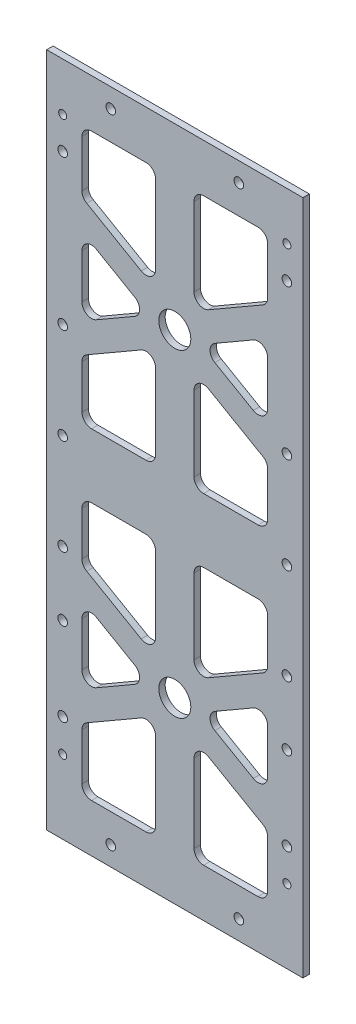
SolidWorks part; units mm, degrees
material "6061-T6 (SS)"
ref_plane "Front Plane" through (0, 0, 0) normal (0, 0, 1) x (1, 0, 0)
ref_plane "Top Plane" through (0, 0, 0) normal (0, 1, 0) x (1, 0, 0)
ref_plane "Right Plane" through (0, 0, 0) normal (1, 0, 0) x (0, 0, -1)
sketch "Sketch1" plane through (0, 0, 0) normal (0, 0, 1) x (1, 0, 0)
  line L1 (0, 0) -> (88, 0)
  line L2 (0, 0) -> (0, 211)
  line L3 (0, 211) -> (88, 211)
  line L4 (88, 0) -> (88, 211)
  dimension "D1" = 88
  dimension "D2" = 211
extrude "Boss-Extrude1" add sketch "Sketch1" along normal blind 2
sketch "Sketch2" plane through (0, 0, 2) normal (0, 0, 1) x (1, 0, 0)
  line L0 (0, 105.5) -> (88, 105.5) construction
  line L1 (0, 211) -> (0, 0) construction
  line L2 (88, 0) -> (88, 211) construction
  line L3 (44, 211) -> (44, 0) construction
  line L4 (88, 211) -> (0, 211) construction
  line L5 (0, 0) -> (88, 0) construction
  line L6 (0, 155.25) -> (88, 155.25) construction
  line L7 (0, 55.75) -> (88, 55.75) construction
  dimension "D1" = 55.75
  dimension "D2" = 55.75
sketch "Sketch3" plane through (0, 0, 2) normal (0, 0, 1) x (1, 0, 0)
  line L0 (0, 155.25) -> (88, 155.25) construction
  line L1 (38, 196) -> (38, 115.5)
  line L2 (0, 211) -> (0, 0) construction
  line L3 (15, 196) -> (73, 196)
  line L4 (15, 196) -> (15, 115.5)
  line L5 (15, 115.5) -> (73, 115.5)
  line L6 (73, 196) -> (73, 115.5)
  line L7 (88, 211) -> (0, 211) construction
  line L8 (88, 0) -> (88, 211) construction
  line L9 (0, 105.5) -> (88, 105.5) construction
  line L13 (73, 171.9932) -> (15, 138.5068) construction
  line L14 (15, 171.9932) -> (73, 138.5068) construction
  line L15 (73, 176.612) -> (15, 143.1256)
  line L16 (73, 167.3744) -> (15, 133.888)
  line L17 (15, 176.612) -> (73, 143.1256)
  line L18 (15, 167.3744) -> (73, 133.888)
  line L19 (50, 196) -> (50, 115.5)
  circle A0 centre (44, 155.25) radius 5
  dimension "D1" = 10
  dimension "D3" = 15
  dimension "D4" = 15
  dimension "D5" = 15
  dimension "D6" = 10
  dimension "D9" = 30
  dimension "D10" = 30
  dimension "D11" = 8
  dimension "D12" = 4
  dimension "D13" = 4
  dimension "D14" = 8
ref_plane "Plane1" through (0, 105.5, 0) normal (0, 1, 0) x (1, 0, 0)
extrude "Cut-Extrude2" cut sketch "Sketch3" against normal blind 2
sketch "Sketch4" plane through (0, 0, 2) normal (0, 0, 1) x (1, 0, 0)
  line L0 (0, 155.25) -> (88, 155.25) construction
  circle A0 centre (44, 155.25) radius 5
  dimension "D1" = 10
extrude "Cut-Extrude3" cut sketch "Sketch4" against normal through all
mirror "Mirror2" about plane through (0, 105.5, 0) normal (0, 1, 0) of "Cut-Extrude2", "Cut-Extrude3"
fillet "Fillet2" radius 3 44 edges at (73, 67.8744, 1) (73, 43.6256, 1) (52, 55.75, 1) (15, 15, 1) (15, 34.388, 1) (15, 143.1256, 1) (15, 167.3744, 1) (36, 155.25, 1) (15, 115.5, 1) (15, 133.888, 1) (73, 196, 1) (73, 115.5, 1) (73, 133.888, 1) (15, 196, 1) (15, 176.612, 1) (73, 167.3744, 1) (73, 143.1256, 1) (52, 155.25, 1) (73, 95.5, 1) (73, 77.112, 1) (73, 34.388, 1) (73, 15, 1) (15, 77.112, 1) (15, 95.5, 1) (15, 43.6256, 1) (15, 67.8744, 1) (36, 55.75, 1) (73, 176.612, 1) (50, 15, 1) (38, 15, 1) (38, 47.6671, 1) (50, 47.6671, 1) (38, 63.8329, 1) (38, 95.5, 1) (50, 63.8329, 1) (50, 95.5, 1) (38, 115.5, 1) (38, 147.1671, 1) (50, 147.1671, 1) (50, 115.5, 1) (38, 196, 1) (38, 163.3329, 1) (50, 163.3329, 1) (50, 196, 1)
sketch "Sketch23" plane through (0, 0, 2) normal (0, 0, 1) x (1, 0, 0)
  line L2 (88, 211) -> (88, 0)
  line L3 (86, 211) -> (86, 0)
  line L4 (86, 211) -> (88, 211)
  line L5 (86, 0) -> (88, 0)
  line L6 (2.1504, 211) -> (2.1504, 0)
  line L7 (2.1504, 211) -> (0, 211)
  line L8 (0, 211) -> (0, 0)
  line L9 (2.1504, 0) -> (0, 0)
  dimension "D1" = 2
extrude "Cut-Extrude5" cut sketch "Sketch23" against normal blind 10 contours L5 L2 L4 L3 | L6 L9 L8 L7
sketch "Sketch29" plane through (0, 0, 0) normal (0, 0, -1) x (-1, 0, 0)
  line L0 (-44, 0) -> (-44, 211)
  line L4 (-86, 105.5) -> (-2.1504, 105.5)
  line L5 (-86, 0) -> (-86, 211) construction
  line L6 (-2.1504, 0) -> (-2.1504, 211) construction
  line L16 (-4, 211) -> (1.9115, 211)
  line L17 (-4, 211) -> (-4, 0)
  line L18 (-4, 0) -> (1.9115, 0)
  line L19 (1.9115, 211) -> (1.9115, 0)
  line L20 (-84, 0) -> (-88.0365, 0)
  line L21 (-84, 0) -> (-84, 211)
  line L22 (-84, 211) -> (-88.0365, 211)
  line L23 (-88.0365, 0) -> (-88.0365, 211)
  point P0 (-44, 155.25)
  point P1 (-44, 217.1483)
  point P3 (-4, 155.25)
  point P4 (-4, 217.1483)
  point P5 (-84, 155.25)
  point P6 (-84, 217.1483)
  point P8 (-4, 105.5)
  point P22 (-84, 105.5)
  point P23 (-44, 105.5)
extrude "Cut-Extrude10" cut sketch "Sketch29" against normal blind 2
sketch "Sketch30" plane through (0, 0, 2) normal (0, 0, 1) x (1, 0, 0)
  line L0 (44, 211) -> (44, 0) construction
  line L1 (84, 211) -> (4, 211) construction
  line L2 (4, 0) -> (84, 0) construction
  line L3 (4, 211) -> (4, 0) construction
  point P8 (64, 6)
  point P9 (79, 23)
  point P10 (79, 33.2)
  point P11 (9, 33.2)
  point P13 (9, 196)
  point P14 (9, 186)
  point P15 (9, 139.2)
  point P16 (9, 109.2)
  point P18 (9, 79.2)
  point P19 (9, 59.2)
  point P20 (79, 59.2)
  point P21 (9, 23)
  point P23 (24, 205)
  point P25 (79, 79.2)
  point P26 (79, 109.2)
  point P27 (24, 6)
  point P29 (79, 139.2)
  point P30 (79, 186)
  point P31 (79, 196)
  point P32 (64, 205)
  dimension "D1" = 20
  dimension "D2" = 6
  dimension "D3" = 5
  dimension "D4" = 15
  dimension "D5" = 25
  dimension "D6" = 71.8
  dimension "D7" = 101.8
  dimension "D8" = 131.8
  dimension "D9" = 151.8
  dimension "D10" = 5
  dimension "D11" = 188
  dimension "D12" = 205
  dimension "D13" = 20
  dimension "D14" = 5
  dimension "D15" = 5
  dimension "D16" = 5
  dimension "D17" = 5
  dimension "D18" = 5
  dimension "D19" = 5
  dimension "D20" = 177.8
hole_wizard "Ø3.0mm Dowel Hole1" positions "Sketch31" profile "Sketch32" hole size "Ø3.0" standard "ANSI Metric" end condition through all
sketch "Sketch31" plane through (0, 0, 2) normal (0, 0, 1) x (1, 0, 0)
  point P0 (24, 205)
  point P3 (64, 205)
  point P6 (9, 186)
  point P9 (79, 186)
  point P12 (9, 139.2)
  point P15 (79, 139.2)
  point P18 (79, 109.2)
  point P21 (9, 109.2)
  point P24 (9, 79.2)
  point P27 (79, 79.2)
  point P30 (79, 59.2)
  point P33 (9, 59.2)
  point P36 (9, 33.2)
  point P39 (79, 33.2)
  point P42 (64, 6)
  point P45 (24, 6)
sketch "Sketch32" plane through (24, 205, 2) normal (1, 0, 0) x (0, -1, 0)
  line L0 (0, 0) -> (0, 2)
  line L1 (0, 2) -> (1.5, 2)
  line L2 (1.5, 2) -> (1.5, 0)
  line L5 (1.5, 0) -> (0, 0)
  line L11 (0, -6.35) -> (0, 107.95) construction
  dimension "Thru Hole Dia." = 3
  dimension "Thru Hole Depth" = 2
hole_wizard "Tap Drill for M3x0.5 Tap1" positions "Sketch33" profile "Sketch34" hole size "M3x0.5" standard "ANSI Metric" end condition through all
sketch "Sketch33" plane through (0, 0, 2) normal (0, 0, 1) x (1, 0, 0)
  point P0 (9, 23)
  point P3 (79, 23)
  point P6 (9, 196)
  point P9 (79, 196)
sketch "Sketch34" plane through (9, 23, 2) normal (1, 0, 0) x (0, -1, 0)
  line L0 (0, 0) -> (0, 2)
  line L1 (0, 2) -> (1.25, 2)
  line L2 (1.25, 2) -> (1.25, 0)
  line L5 (1.25, 0) -> (0, 0)
  line L11 (0, -6.35) -> (0, 107.95) construction
  dimension "Thru Hole Dia." = 2.5
  dimension "Thru Hole Depth" = 2
equation "\"stack_house_hole_distance\"=15"
equation "\"battery_top_clearance\"=15"
equation "\"coils_top_clearance\"=10"
